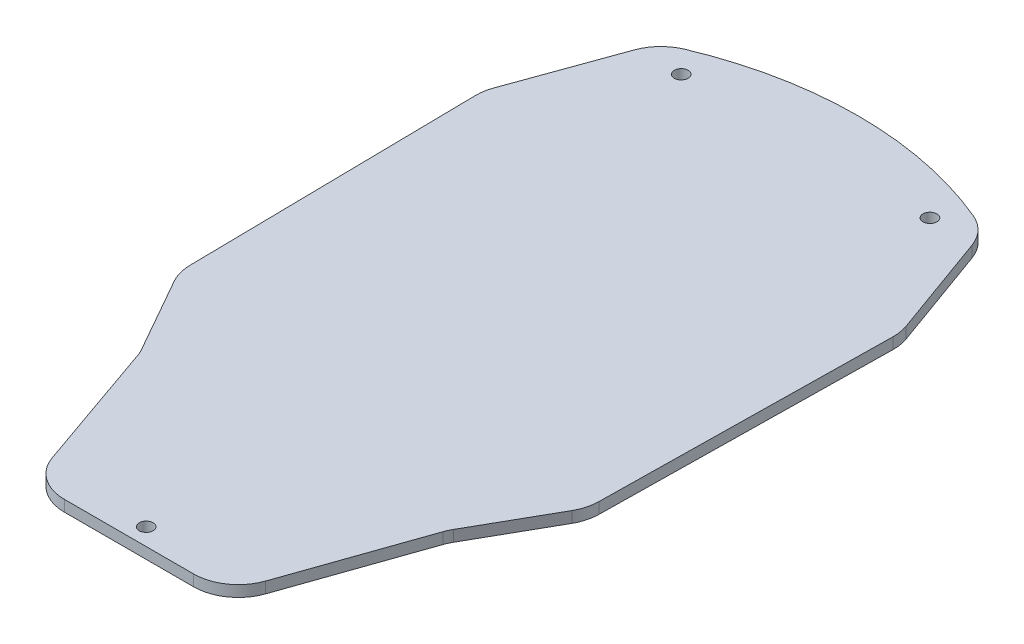
SolidWorks part; units mm, degrees
ref_plane "Front" through (0, 0, 0) normal (0, 0, 1) x (1, 0, 0)
ref_plane "Top" through (0, 0, 0) normal (0, 1, 0) x (1, 0, 0)
ref_plane "Right" through (0, 0, 0) normal (1, 0, 0) x (0, 0, -1)
sketch "Sketch1" plane through (0, 0, 0) normal (0, 1, 0) x (1, 0, 0)
  line L0 (0, 0) -> (0, 93.3456) construction
  line L1 (-28.575, 0) -> (28.575, 0) construction
  line L2 (-45.339, 47.9542) -> (45.339, 47.9542) construction
  line L3 (28.575, 0) -> (45.339, 47.9542) construction
  line L4 (-61.1695, 162.4185) -> (-47.625, 199.9259) construction
  line L5 (45.339, 47.9542) -> (59.8424, 73.5285) construction
  line L6 (59.8424, 73.5285) -> (61.1695, 162.4185) construction
  line L7 (61.1695, 162.4185) -> (47.625, 199.9259) construction
  line L8 (-59.8424, 73.5285) -> (-61.1695, 162.4185) construction
  line L9 (-45.339, 47.9542) -> (-59.8424, 73.5285) construction
  line L10 (-28.575, 0) -> (-45.339, 47.9542) construction
  line L11 (-58.2611, 73.9583) -> (-59.5779, 162.1522)
  line L12 (-59.5779, 162.1522) -> (-46.3505, 198.7813)
  line L13 (59.5779, 162.1522) -> (46.3505, 198.7813)
  line L14 (58.2611, 73.9583) -> (59.5779, 162.1522)
  line L15 (43.8876, 48.613) -> (58.2611, 73.9583)
  line L16 (27.4483, 1.5875) -> (43.8876, 48.613)
  line L17 (-27.4483, 1.5875) -> (27.4483, 1.5875)
  line L18 (-27.4483, 1.5875) -> (-43.8876, 48.613)
  line L19 (-43.8876, 48.613) -> (-58.2611, 73.9583)
  arc A0 (-47.625, 199.9259) -> (47.625, 199.9259) centre (0, 103.0493) cw construction
  arc A1 (-46.3505, 198.7813) -> (46.3505, 198.7813) centre (0, 103.0493) cw
  point P9 (0, 47.9542)
  point P15 (0, 0)
  dimension "D10" = 107.95
  dimension "D1" = 28.575
  dimension "D2" = 45.339
  dimension "D3" = 59.8424
  dimension "D4" = 29.4005
  dimension "D5" = 50.8
  dimension "D6" = 88.9
  dimension "D7" = 39.878
  dimension "D8" = 61.1695
  dimension "D9" = 47.625
  dimension "D11" = 1.5875
extrude "Boss-Extrude1" add sketch "Sketch1" along normal blind 3.175 contours A1 L13 L14 L15 L16 L17 L18 L19 L11 L12
hole_wizard "5/32 (0.15625) Diameter Hole1" positions "Sketch3" profile "Sketch2" hole size "5/32" standard "ANSI Inch" end condition through all
sketch "Sketch3" plane through (0, 3.175, 0) normal (0, 1, 0) x (1, 0, 0)
  line L0 (-27.4483, 1.5875) -> (27.4483, 1.5875) construction
  line L2 (0, 209.4118) -> (0, 0) construction
  arc A0 (46.3505, 198.7813) -> (-46.3505, 198.7813) centre (0, 103.0493) ccw construction
  point P0 (0, 6.4834)
  point P2 (-35.452, 194.4496)
  point P4 (35.452, 194.4496)
  point P7 (0, 1.5875)
  dimension "D1" = 4.8959
  dimension "D2" = 70.9041
  dimension "D3" = 122.6312
sketch "Sketch2" plane through (0, 3.175, -6.4834) normal (1, 0, 0) x (0, 0, 1)
  line L0 (0, 0) -> (0, 3.175)
  line L1 (0, 3.175) -> (1.9844, 3.175)
  line L2 (1.9844, 3.175) -> (1.9844, 0)
  line L5 (1.9844, 0) -> (0, 0)
  line L11 (0, -6.35) -> (0, 107.95) construction
  dimension "Thru Hole Dia." = 3.9688
  dimension "Thru Hole Depth" = 3.175
fillet "Fillet1" radius 12.7 10 edges at (-46.3505, 1.5875, -198.7813) (46.3505, 1.5875, -198.7813) (59.5779, 1.5875, -162.1522) (58.2611, 1.5875, -73.9583) (43.8876, 1.5875, -48.613) (27.4483, 1.5875, -1.5875) (-43.8876, 1.5875, -48.613) (-58.2611, 1.5875, -73.9583) (-59.5779, 1.5875, -162.1522) (-27.4483, 1.5875, -1.5875)
